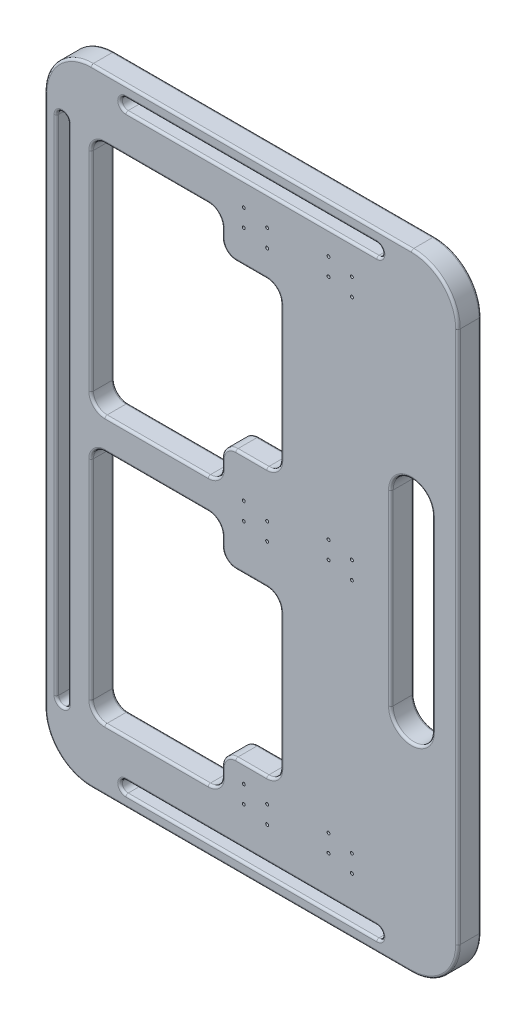
SolidWorks part; units mm, degrees
material "PVC Rigid"
ref_plane "Front Plane" through (0, 0, 0) normal (0, 0, 1) x (1, 0, 0)
ref_plane "Top Plane" through (0, 0, 0) normal (0, 1, 0) x (1, 0, 0)
ref_plane "Right Plane" through (0, 0, 0) normal (1, 0, 0) x (0, 0, -1)
sketch "Sketch1" plane through (0, 0, 0) normal (0, 0, 1) x (1, 0, 0)
  line L0 (9.525, -337.1515) -> (0, -337.1515) construction
  line L3 (4.7625, -385.4251) -> (4.7625, -288.878) construction
  line L7 (178.8413, 5.8307) -> (-169.3163, 5.8307)
  line L8 (229.3467, -44.6747) -> (229.3467, -624.1674)
  line L9 (178.8413, -674.6729) -> (-169.3163, -674.6729)
  line L10 (-219.8217, -44.6747) -> (-219.8217, -624.1674)
  line L11 (229.3467, -334.4211) -> (-219.8217, -334.4211) construction
  line L12 (178.8413, 5.8307) -> (178.8413, -674.6729) construction
  line L13 (178.8413, -232.8211) -> (178.8413, -436.0211) construction
  line L14 (201.2772, -232.8211) -> (201.2772, -436.0211)
  line L15 (156.4054, -232.8211) -> (156.4054, -436.0211)
  line L16 (-131.5196, -13.2193) -> (141.0446, -13.2193) construction
  line L17 (-42.0217, -61.0845) -> (-154.3708, -61.0845)
  line L18 (-27.0763, -76.0299) -> (-27.0763, -85.6213)
  line L19 (-42.0217, -317.5) -> (-154.3708, -317.5)
  line L20 (-169.3163, -76.0299) -> (-169.3163, -302.5546)
  line L23 (-131.5196, -6.8693) -> (141.0446, -6.8693)
  line L24 (-131.5196, -19.5693) -> (141.0446, -19.5693)
  line L28 (-169.3163, 5.8307) -> (-169.3163, -334.4211) construction
  line L30 (-27.0763, -292.9631) -> (-27.0763, -302.5546)
  line L31 (-12.1308, -100.5668) -> (21.4783, -100.5668)
  line L33 (-12.1308, -278.0177) -> (21.4783, -278.0177)
  line L34 (36.4237, -115.5122) -> (36.4237, -263.0723)
  line L35 (-27.0763, -375.879) -> (-27.0763, -366.2876)
  line L36 (-42.0217, -351.3421) -> (-154.3708, -351.3421)
  line L37 (-169.3163, -592.8122) -> (-169.3163, -366.2876)
  line L38 (-42.0217, -607.7577) -> (-154.3708, -607.7577)
  line L39 (-27.0763, -592.8122) -> (-27.0763, -583.2208)
  line L40 (-12.1308, -568.2754) -> (21.4783, -568.2754)
  line L41 (36.4237, -553.3299) -> (36.4237, -405.7699)
  line L42 (-12.1308, -390.8244) -> (21.4783, -390.8244)
  line L43 (-200.7717, -607.7577) -> (-200.7717, -61.0845) construction
  line L44 (-207.1217, -607.7577) -> (-207.1217, -61.0845)
  line L45 (-194.4217, -607.7577) -> (-194.4217, -61.0845)
  line L46 (-131.5196, -655.6229) -> (141.0446, -655.6229) construction
  line L47 (-131.5196, -661.9729) -> (141.0446, -661.9729)
  line L48 (-131.5196, -649.2729) -> (141.0446, -649.2729)
  arc A0 (-169.3163, -674.6729) -> (-219.8217, -624.1674) centre (-169.3163, -624.1674) cw
  arc A1 (229.3467, -624.1674) -> (178.8413, -674.6729) centre (178.8413, -624.1674) cw
  arc A2 (178.8413, 5.8307) -> (229.3467, -44.6747) centre (178.8413, -44.6747) cw
  arc A3 (-169.3163, 5.8307) -> (-219.8217, -44.6747) centre (-169.3163, -44.6747) ccw
  arc A4 (201.2772, -232.8211) -> (156.4054, -232.8211) centre (178.8413, -232.8211) ccw
  arc A5 (156.4054, -436.0211) -> (201.2772, -436.0211) centre (178.8413, -436.0211) ccw
  arc A6 (-131.5196, -6.8693) -> (-131.5196, -19.5693) centre (-131.5196, -13.2193) ccw
  arc A7 (141.0446, -19.5693) -> (141.0446, -6.8693) centre (141.0446, -13.2193) ccw
  arc A10 (21.4783, -100.5668) -> (36.4237, -115.5122) centre (21.4783, -115.5122) cw
  arc A11 (21.4783, -278.0177) -> (36.4237, -263.0723) centre (21.4783, -263.0723) ccw
  arc A12 (-27.0763, -292.9631) -> (-12.1308, -278.0177) centre (-12.1308, -292.9631) cw
  arc A13 (-27.0763, -302.5546) -> (-42.0217, -317.5) centre (-42.0217, -302.5546) cw
  arc A14 (-154.3708, -317.5) -> (-169.3163, -302.5546) centre (-154.3708, -302.5546) cw
  arc A15 (-154.3708, -61.0845) -> (-169.3163, -76.0299) centre (-154.3708, -76.0299) ccw
  arc A16 (-42.0217, -61.0845) -> (-27.0763, -76.0299) centre (-42.0217, -76.0299) cw
  arc A17 (-27.0763, -85.6213) -> (-12.1308, -100.5668) centre (-12.1308, -85.6213) ccw
  arc A18 (-27.0763, -366.2876) -> (-42.0217, -351.3421) centre (-42.0217, -366.2876) ccw
  arc A19 (-154.3708, -351.3421) -> (-169.3163, -366.2876) centre (-154.3708, -366.2876) ccw
  arc A20 (-154.3708, -607.7577) -> (-169.3163, -592.8122) centre (-154.3708, -592.8122) cw
  arc A21 (-42.0217, -607.7577) -> (-27.0763, -592.8122) centre (-42.0217, -592.8122) ccw
  arc A22 (-27.0763, -583.2208) -> (-12.1308, -568.2754) centre (-12.1308, -583.2208) cw
  arc A23 (21.4783, -568.2754) -> (36.4237, -553.3299) centre (21.4783, -553.3299) ccw
  arc A24 (21.4783, -390.8244) -> (36.4237, -405.7699) centre (21.4783, -405.7699) cw
  arc A25 (-27.0763, -375.879) -> (-12.1308, -390.8244) centre (-12.1308, -375.879) ccw
  arc A26 (-207.1217, -607.7577) -> (-194.4217, -607.7577) centre (-200.7717, -607.7577) ccw
  arc A27 (-194.4217, -61.0845) -> (-207.1217, -61.0845) centre (-200.7717, -61.0845) ccw
  arc A28 (-131.5196, -661.9729) -> (-131.5196, -649.2729) centre (-131.5196, -655.6229) cw
  arc A29 (141.0446, -649.2729) -> (141.0446, -661.9729) centre (141.0446, -655.6229) cw
  point P12 (4.7625, -337.1515)
  point P31 (178.8413, -334.4211)
  point P47 (4.7625, -13.2193)
  point P53 (4.7625, -38.6193)
  point P64 (36.4237, -100.5668)
  point P65 (-27.0763, -189.2922)
  point P78 (-169.3163, -61.0845)
  point P81 (-27.0763, -61.0845)
  point P84 (-27.0763, -100.5668)
  point P111 (-200.7717, -334.4211)
  point P118 (4.7625, -655.6229)
  point P125 (4.7625, -630.2229)
  dimension "D1" = 50.5054
  dimension "D7" = 14.9454
  dimension "D2" = 203.2
  dimension "D3" = 12.7
  dimension "D5" = 142.24
  dimension "D6" = 63.5
  dimension "D8" = 12.7
  dimension "D9" = 12.7
  dimension "D10" = 12.7
extrude "Boss-Extrude1" add sketch "Sketch1" along normal blind 25.4
fillet "Fillet1" radius 2.54 112 edges at (147.3946, -655.6229, 0) (4.7625, -661.9729, 0) (-137.8696, -655.6229, 0) (4.7625, -649.2729, 0) (-200.7717, -54.7345, 0) (-194.4217, -334.4211, 0) (-200.7717, -614.1077, 0) (-207.1217, -334.4211, 0) (32.0463, -395.2018, 0) (36.4237, -479.5499, 0) (32.0463, -563.8979, 0) (4.6737, -568.2754, 0) (-22.6989, -572.6528, 0) (-27.0763, -588.0165, 0) (-31.4537, -603.3802, 0) (-98.1963, -607.7577, 0) (-164.9389, -603.3802, 0) (-169.3163, -479.5499, 0) (-164.9389, -355.7195, 0) (-98.1963, -351.3421, 0) (-31.4537, -355.7195, 0) (-27.0763, -371.0833, 0) (-22.6989, -386.447, 0) (4.6737, -390.8244, 0) (32.0463, -273.6403, 0) (4.6737, -278.0177, 0) (-22.6989, -282.3951, 0) (-27.0763, -297.7588, 0) (-31.4537, -313.1226, 0) (-98.1963, -317.5, 0) (-164.9389, -313.1226, 0) (-169.3163, -189.2922, 0) (-164.9389, -65.4619, 0) (-98.1963, -61.0845, 0) (-31.4537, -65.4619, 0) (-27.0763, -80.8256, 0) (-22.6989, -96.1893, 0) (4.6737, -100.5668, 0) (32.0463, -104.9442, 0) (36.4237, -189.2922, 0) (147.3946, -13.2193, 0) (4.7625, -19.5693, 0) (-137.8696, -13.2193, 0) (4.7625, -6.8693, 0) (178.8413, -458.457, 0) (156.4054, -334.4211, 0) (178.8413, -210.3852, 0) (201.2772, -334.4211, 0) (4.7625, -674.6729, 0) (214.554, -659.8802, 0) (229.3467, -334.4211, 0) (214.554, -8.962, 0) (4.7625, 5.8307, 0) (-205.029, -8.962, 0) (-219.8217, -334.4211, 0) (-205.029, -659.8802, 0) (-194.4217, -334.4211, 25.4) (-200.7717, -54.7345, 25.4) (-207.1217, -334.4211, 25.4) (-200.7717, -614.1077, 25.4) (4.6737, -100.5668, 25.4) (-22.6989, -96.1893, 25.4) (-27.0763, -80.8256, 25.4) (-31.4537, -65.4619, 25.4) (-98.1963, -61.0845, 25.4) (-164.9389, -65.4619, 25.4) (-169.3163, -189.2922, 25.4) (-164.9389, -313.1226, 25.4) (-98.1963, -317.5, 25.4) (-31.4537, -313.1226, 25.4) (-27.0763, -297.7588, 25.4) (-22.6989, -282.3951, 25.4) (4.6737, -278.0177, 25.4) (32.0463, -273.6403, 25.4) (36.4237, -189.2922, 25.4) (32.0463, -104.9442, 25.4) (4.7625, -19.5693, 25.4) (147.3946, -13.2193, 25.4) (4.7625, -6.8693, 25.4) (-137.8696, -13.2193, 25.4) (-219.8217, -334.4211, 25.4) (-205.029, -8.962, 25.4) (4.7625, 5.8307, 25.4) (214.554, -8.962, 25.4) (229.3467, -334.4211, 25.4) (214.554, -659.8802, 25.4) (4.7625, -674.6729, 25.4) (-205.029, -659.8802, 25.4) (156.4054, -334.4211, 25.4) (178.8413, -458.457, 25.4) (201.2772, -334.4211, 25.4) (178.8413, -210.3852, 25.4) (-27.0763, -371.0833, 25.4) (-31.4537, -355.7195, 25.4) (-98.1963, -351.3421, 25.4) (-164.9389, -355.7195, 25.4) (-169.3163, -479.5499, 25.4) (-164.9389, -603.3802, 25.4) (-98.1963, -607.7577, 25.4) (-31.4537, -603.3802, 25.4) (-27.0763, -588.0165, 25.4) (-22.6989, -572.6528, 25.4) (4.6737, -568.2754, 25.4) (32.0463, -563.8979, 25.4) (36.4237, -479.5499, 25.4) (32.0463, -395.2018, 25.4) (4.6737, -390.8244, 25.4) (-22.6989, -386.447, 25.4) (4.7625, -661.9729, 25.4) (147.3946, -655.6229, 25.4) (4.7625, -649.2729, 25.4) (-137.8696, -655.6229, 25.4)
hole_wizard "Hole2" positions "Sketch9" profile "Sketch10" legacy
sketch "Sketch9" plane through (0, 0, 0) normal (0, 0, -1) x (-1, 0, 0)
  point P0 (-114.0534, -52.004)
  point P3 (-114.0534, -71.054)
  point P6 (-88.6534, -45.654)
  point P9 (-88.6534, -64.704)
  point P12 (3.4216, -45.654)
  point P15 (3.4216, -64.704)
  point P18 (-21.9784, -52.004)
  point P21 (-21.9784, -71.054)
  point P24 (-21.9784, -328.0711)
  point P27 (-21.9784, -347.1211)
  point P30 (3.4216, -340.7711)
  point P33 (3.4216, -321.7211)
  point P49 (-114.0534, -594.5702)
  point P52 (-114.0534, -613.6202)
  point P55 (-88.6534, -607.2702)
  point P58 (-88.6534, -588.2202)
  point P61 (3.4216, -588.2202)
  point P64 (3.4216, -607.2702)
  point P67 (-21.9784, -594.5702)
  point P70 (-21.9784, -613.6202)
  point P74 (-114.0534, -337.5531)
  point P77 (-114.0534, -318.5031)
  point P80 (-88.6534, -331.2031)
  point P83 (-88.6534, -312.1531)
sketch "Sketch10" plane through (114.0534, -52.004, 0) normal (1, 0, 0) x (0, 1, 0)
  line L0 (0, 0) -> (0, 31.75)
  line L1 (0, 31.75) -> (1.5875, 31.75)
  line L2 (1.5875, 31.75) -> (1.5875, 3.5052)
  line L3 (1.5875, 3.5052) -> (2.8702, 3.5052)
  line L4 (2.8702, 3.5052) -> (2.8702, 0)
  line L5 (2.8702, 0) -> (0, 0)
  line L6 (0, 110) -> (0, -10) construction
  dimension "Diameter" = 3.175
  dimension "Depth" = 31.75
  dimension "C-Bore Diameter" = 5.7404
  dimension "C-Bore Depth" = 3.5052
